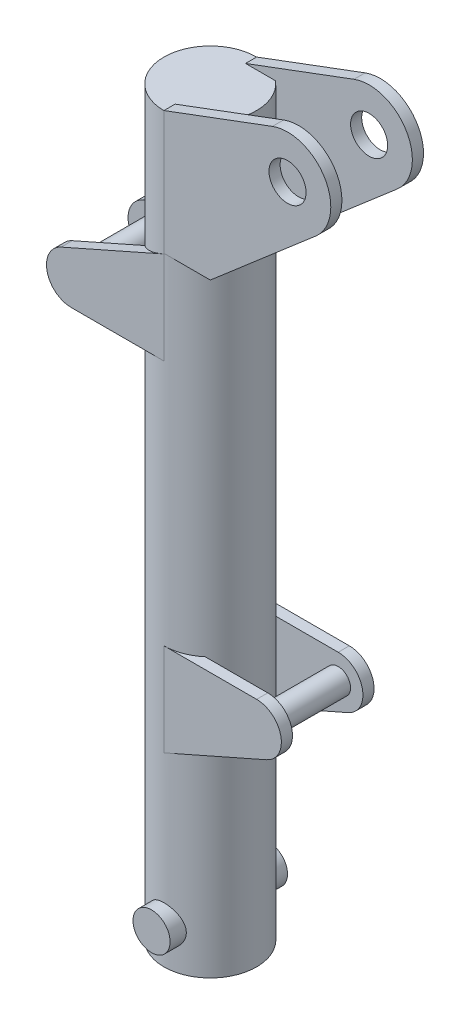
SolidWorks part; units mm, degrees
material "AISI 4340 Steel, normalized"
ref_plane "Front Plane" through (0, 0, 0) normal (0, 0, 1) x (1, 0, 0)
ref_plane "Top Plane" through (0, 0, 0) normal (0, 1, 0) x (1, 0, 0)
ref_plane "Right Plane" through (0, 0, 0) normal (1, 0, 0) x (0, 0, -1)
sketch "Sketch2" plane through (0, 0, 0) normal (0, 1, 0) x (1, 0, 0)
  circle A0 centre (0, 0) radius 75
  dimension "D1" = 150
extrude "Boss-Extrude1" add sketch "Sketch2" along normal blind 1200
shell "Shell4" thickness 10
ref_plane "Plane2" through (0, 0, 75) normal (0, 0, 1) x (1, 0, 0)
sketch "Sketch3" plane through (0, 0, 0) normal (0, 0, 1) x (1, 0, 0)
  line L0 (0, 450) -> (150, 450)
  line L2 (0, 300) -> (0, 450)
  line L3 (0, 300) -> (166.1647, 373.4117)
  line L4 (0, 999) -> (0, 849)
  line L5 (0, 849) -> (-150, 849)
  line L6 (0, 999) -> (-166.1647, 925.5883)
  line L7 (75, 1200) -> (-75, 1200) construction
  line L17 (0, 1000) -> (0, 1200)
  line L18 (0, 1200) -> (175.5, 1265.5725)
  line L20 (245.6739, 1146.9538) -> (75, 1000)
  line L21 (75, 0) -> (75, 1200) construction
  line L22 (75, 1000) -> (0, 1000)
  line L23 (0, 1200) -> (200, 1200) construction
  arc A0 (166.1647, 373.4117) -> (150, 450) centre (150, 410) ccw
  circle A1 centre (150, 410) radius 20 construction
  arc A2 (-166.1647, 925.5883) -> (-150, 849) centre (-150, 889) ccw
  circle A3 centre (-150, 889) radius 20 construction
  circle A7 centre (200, 1200) radius 30
  arc A8 (245.6739, 1146.9538) -> (175.5, 1265.5725) centre (200, 1200) ccw
  dimension "D1" = 40
  dimension "D2" = 20
  dimension "D3" = 150
  dimension "D6" = 20
  dimension "D7" = 40
  dimension "D11" = 60
  dimension "D12" = 40
  dimension "D4" = 300
  dimension "D5" = 150
  dimension "D8" = 201
  dimension "D9" = 150
  dimension "D10" = 150
  dimension "D13" = 200
  dimension "D14" = 200
extrude "Boss-Extrude2" add sketch "Sketch3" against normal blind 18 from surface at 75 starting at plane "Plane2"
sketch "Sketch10" plane through (0, 0, 0) normal (0, 0, 1) x (1, 0, 0)
  circle A0 centre (0, 60) radius 30
  dimension "D1" = 60
  dimension "D2" = 60
sketch "Sketch11" plane through (0, 0, 0) normal (0, -1, 0) x (1, 0, 0)
  line L0 (0, 0) -> (-75, 0) construction
  line L1 (-75, 0) -> (75, 0) construction
  circle A0 centre (0, 0) radius 75 construction
ref_plane "Plane4" through (0, 0, 0) normal (0, 0, -1) x (-1, 0, 0)
mirror "Mirror11" about plane through (0, 0, 0) normal (0, 0, -1) of "Boss-Extrude2"
extrude "Boss-Extrude3" add sketch "Sketch10" along normal mid plane 190
sketch "Sketch12" plane through (0, 0, 0) normal (0, 0, 1) x (1, 0, 0)
  circle A0 centre (150, 410) radius 20 construction
  circle A2 centre (-150, 889) radius 20 construction
  circle A3 centre (150, 410) radius 20
  circle A5 centre (-150, 889) radius 20
extrude "Boss-Extrude4" add sketch "Sketch12" along normal mid plane 150
